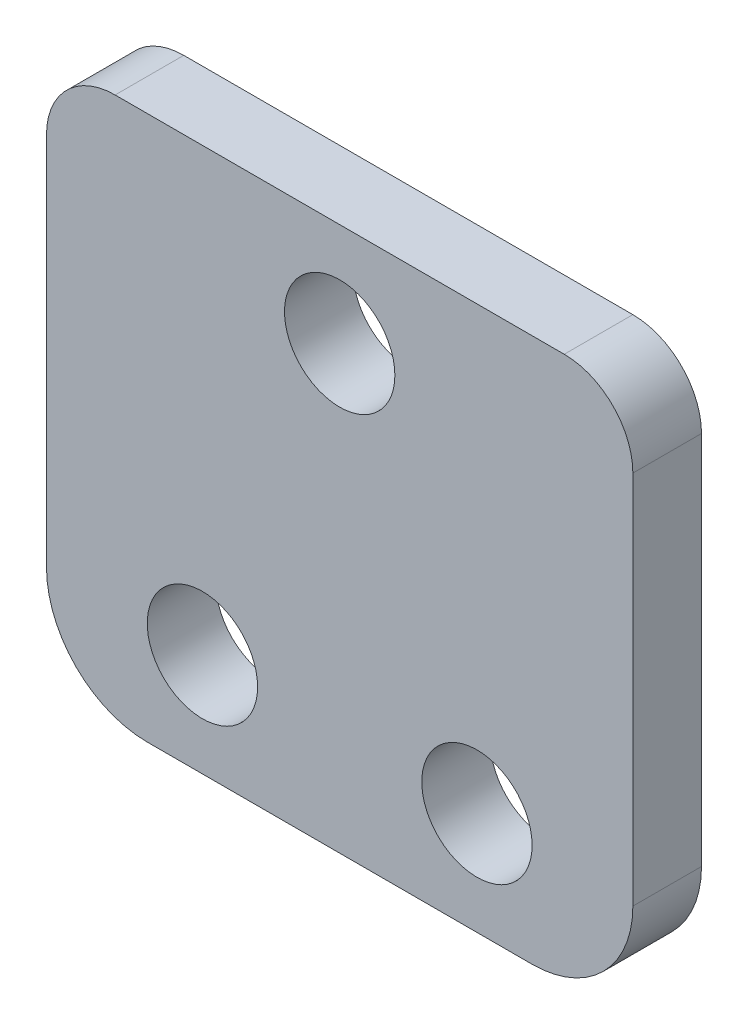
SolidWorks part; units mm, degrees
ref_plane "Front Plane" through (0, 0, 0) normal (0, 0, 1) x (1, 0, 0)
ref_plane "Top Plane" through (0, 0, 0) normal (0, 1, 0) x (1, 0, 0)
ref_plane "Right Plane" through (0, 0, 0) normal (1, 0, 0) x (0, 0, -1)
sketch "Sketch1" plane through (0, 0, 0) normal (0, 0, 1) x (1, 0, 0)
  line L1 (8.9027, 4.6609) -> (-8.9027, 4.6609)
  line L3 (10.3886, -4.6609) -> (-10.3886, -4.6609)
  line L6 (8.9027, 4.6609) -> (-8.9027, 4.6609)
  line L7 (-8.9027, -4.6609) -> (8.9027, -4.6609)
  line L8 (13.5636, -1.4859) -> (13.5636, 17.3482)
  line L9 (10.3886, 20.5232) -> (-10.3886, 20.5232)
  line L10 (-13.5636, -1.4859) -> (-13.5636, 17.3482)
  arc A0 (13.5636, 17.3482) -> (10.3886, 20.5232) centre (10.3886, 17.3482) ccw
  arc A1 (-10.3886, 20.5232) -> (-13.5636, 17.3482) centre (-10.3886, 17.3482) ccw
  arc A4 (8.9027, -4.6609) -> (8.9027, 4.6609) centre (8.9027, 0) ccw
  arc A5 (-8.9027, 4.6609) -> (-8.9027, -4.6609) centre (-8.9027, 0) ccw
  arc A6 (-10.3886, -4.6609) -> (-13.5636, -1.4859) centre (-10.3886, -1.4859) cw
  arc A7 (10.3886, -4.6609) -> (13.5636, -1.4859) centre (10.3886, -1.4859) ccw
  dimension "D2" = 3.175
extrude "Boss-Extrude1" add sketch "Sketch1" along normal blind 3.175 contours A5 L1 A4 L8 A0 L9 A1 L10 | L1 A5 L3 A4
hole_wizard "#10 Clearance Hole1" positions "Sketch2" profile "Sketch3" hole size "#10" standard "ANSI Inch" end condition through all
sketch "Sketch2" plane through (0, 0, 3.175) normal (0, 0, 1) x (1, 0, 0)
  line L0 (0, -4.6609) -> (0, 20.5232) construction
  line L1 (8.9027, -4.6609) -> (-8.9027, -4.6609) construction
  line L2 (10.3886, 20.5232) -> (-10.3886, 20.5232) construction
  line L4 (6.35, 0.1016) -> (-6.35, 0.1016) construction
  point P0 (6.35, 0.1016)
  point P2 (-6.35, 0.1016)
  point P4 (0, 15.7607)
  point P21 (0, 0.1016)
  dimension "D1" = 12.7
  dimension "D2" = 4.7625
  dimension "D3" = 4.7625
sketch "Sketch3" plane through (6.35, 0.1016, 3.175) normal (1, 0, 0) x (0, -1, 0)
  line L0 (0, 0) -> (0, 3.175)
  line L1 (0, 3.175) -> (2.5527, 3.175)
  line L2 (2.5527, 3.175) -> (2.5527, 0)
  line L5 (2.5527, 0) -> (0, 0)
  line L11 (0, -6.35) -> (0, 107.95) construction
  dimension "Thru Hole Dia." = 5.1054
  dimension "Thru Hole Depth" = 3.175
